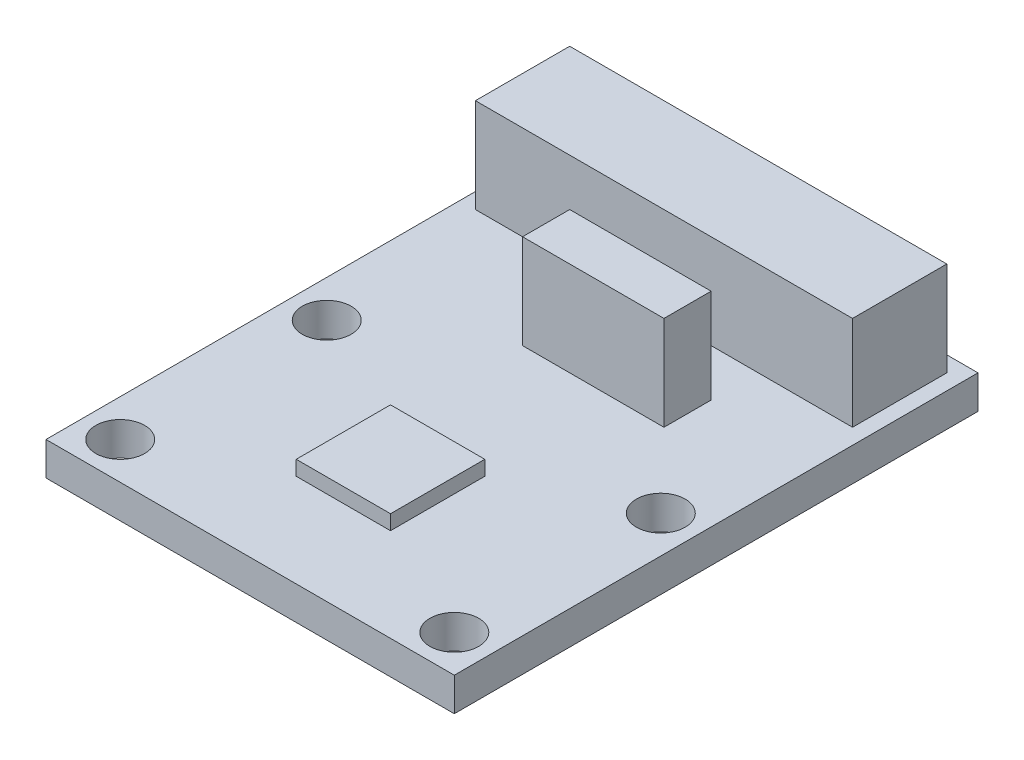
SolidWorks part; units mm, degrees
ref_plane "Front Plane" through (0, 0, 0) normal (0, 0, 1) x (1, 0, 0)
ref_plane "Top Plane" through (0, 0, 0) normal (0, 1, 0) x (1, 0, 0)
ref_plane "Right Plane" through (0, 0, 0) normal (1, 0, 0) x (0, 0, -1)
sketch "Sketch1" plane through (0, 0, 0) normal (0, 1, 0) x (1, 0, 0)
  line L0 (-9, -5.5625) -> (-11, -7.5625) construction
  line L9 (-9, 5.5625) -> (9, -5.5625) construction
  line L11 (-9, 5.5625) -> (9, 5.5625) construction
  line L12 (-9, 5.5625) -> (-9, -5.5625) construction
  line L13 (-9, -5.5625) -> (9, -5.5625) construction
  line L14 (9, 5.5625) -> (9, -5.5625) construction
  line L15 (9, -5.5625) -> (11, -7.5625) construction
  line L17 (-11, -7.5625) -> (11, -7.5625)
  line L18 (-11, -7.5625) -> (-11, 20.6542)
  line L19 (-11, 20.6542) -> (11, 20.6542)
  line L20 (11, -7.5625) -> (11, 20.6542)
  line L21 (-11, -7.5625) -> (11, 20.6542) construction
  line L22 (-11, 20.6542) -> (11, -7.5625) construction
  circle A0 centre (-9, 5.5625) radius 1.315
  circle A1 centre (9, 5.5625) radius 1.315
  circle A2 centre (9, -5.5625) radius 1.315
  circle A3 centre (-9, -5.5625) radius 1.315
  point P0 (0, 6.5458)
  point P4 (0, 0)
  dimension "D3" = 2.63
  dimension "D1" = 28.2167
  dimension "D4" = 18
  dimension "D5" = 11.125
  dimension "D6" = 22
extrude "Boss-Extrude1" add sketch "Sketch1" along normal blind 1.8
sketch "Sketch2" plane through (0, 1.8, 0) normal (0, 1, 0) x (1, 0, 0)
  line L10 (-2.54, -2.54) -> (2.54, -2.54)
  line L11 (-2.54, -2.54) -> (-2.54, 2.54)
  line L12 (-2.54, 2.54) -> (2.54, 2.54)
  line L13 (2.54, -2.54) -> (2.54, 2.54)
  line L14 (-2.54, -2.54) -> (2.54, 2.54) construction
  line L15 (-2.54, 2.54) -> (2.54, -2.54) construction
  point P0 (0, 0)
  dimension "D1" = 5.08
extrude "Boss-Extrude2" add sketch "Sketch2" along normal blind 0.7937
sketch "Sketch3" plane through (0, 0, 0) normal (0, -1, 0) x (-1, 0, 0)
  line L0 (-11, 20.6542) -> (-10.16, 19.8142) construction
  line L1 (-5.08, 12.1942) -> (2.54, 12.1942)
  line L2 (-5.08, 12.1942) -> (-5.08, 9.6542)
  line L3 (-5.08, 9.6542) -> (2.54, 9.6542)
  line L4 (2.54, 12.1942) -> (2.54, 9.6542)
  line L5 (-5.08, 12.1942) -> (2.54, 9.6542) construction
  line L6 (-5.08, 9.6542) -> (2.54, 12.1942) construction
  line L7 (-10.16, 19.8142) -> (10.16, 19.8142)
  line L8 (-10.16, 19.8142) -> (-10.16, 14.7342)
  line L9 (-10.16, 14.7342) -> (10.16, 14.7342)
  line L10 (10.16, 19.8142) -> (10.16, 14.7342)
  line L11 (-10.16, 19.8142) -> (10.16, 14.7342) construction
  line L12 (-10.16, 14.7342) -> (10.16, 19.8142) construction
  line L13 (10.16, 19.8142) -> (11, 20.6542) construction
  point P4 (-1.27, 10.9242)
  point P9 (0, 17.2742)
  dimension "D1" = 20.32
  dimension "D2" = 5.08
  dimension "D3" = 2.54
  dimension "D4" = 7.62
  dimension "D5" = 1.27
  dimension "D6" = 2.54
extrude "Boss-Extrude3" add sketch "Sketch3" against normal blind 5.08 from surface at -1.8 starting at face at (-9, 1.8, 6.8775)
equation "\"PINWIDTH\"= .1"
equation "\"D1@Sketch3\"=\"PINWIDTH\"*8"
equation "\"D2@Sketch3\"=\"PINWIDTH\"*2"
equation "\"D3@Sketch3\"=\"PINWIDTH\""
equation "\"D4@Sketch3\"=\"PINWIDTH\"*3"
equation "\"D5@Sketch3\"=\"PINWIDTH\"*.5"
